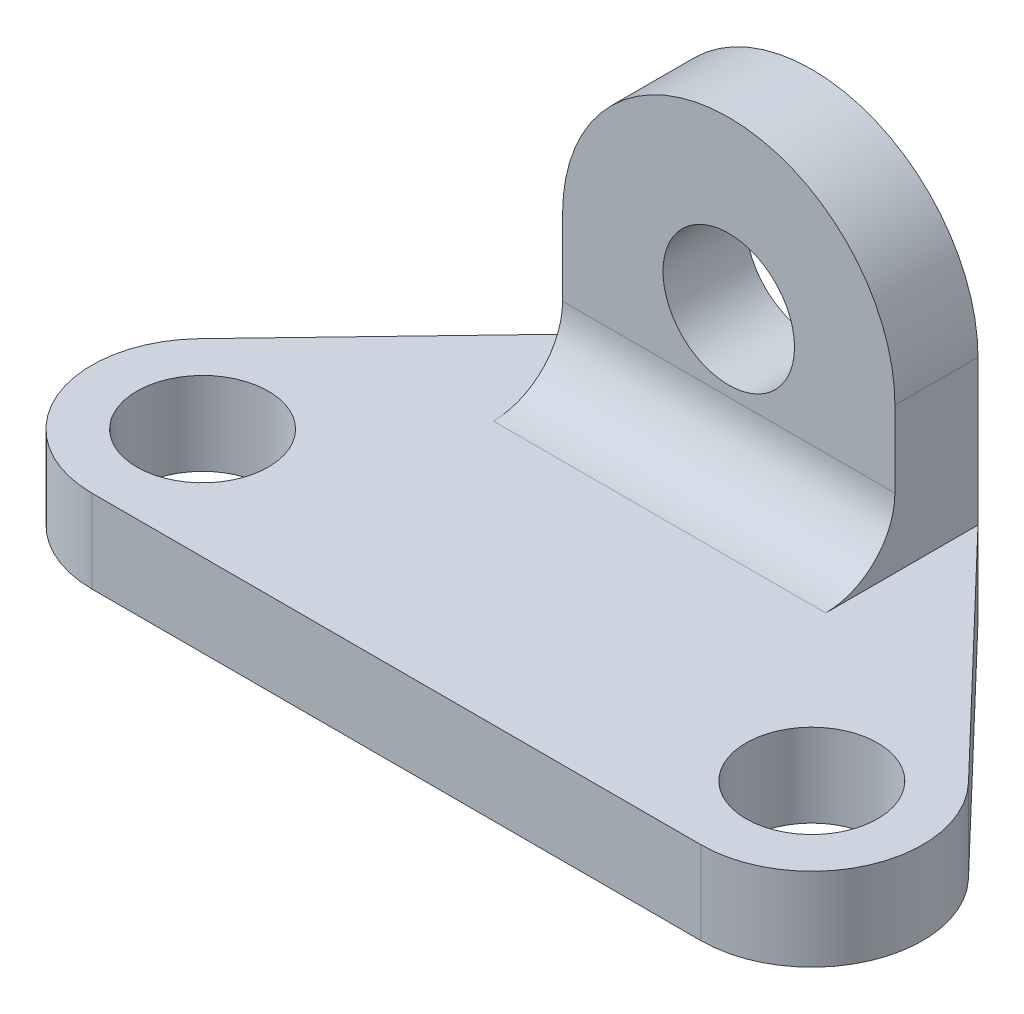
SolidWorks part; units mm, degrees
ref_plane "정면" through (0, 0, 0) normal (0, 0, 1) x (1, 0, 0)
ref_plane "윗면" through (0, 0, 0) normal (0, 1, 0) x (1, 0, 0)
ref_plane "우측면" through (0, 0, 0) normal (1, 0, 0) x (0, 0, -1)
sketch "스케치8" plane through (0, 0, 0) normal (0, 1, 0) x (1, 0, 0)
  line L0 (-44, -16) -> (44, -16)
  line L1 (-55.5528, 11.0695) -> (-24, 44)
  line L2 (-24, 44) -> (24, 44)
  line L3 (24, 44) -> (55.5528, 11.0695)
  arc A0 (-55.5528, 11.0695) -> (-44, -16) centre (-44, 0) ccw
  arc A1 (44, -16) -> (55.5528, 11.0695) centre (44, 0) ccw
  point P12 (44, 0)
  point P13 (41.7229, -13.9714)
  dimension "D1" = 32
  dimension "D2" = 32
  dimension "D8" = 0
  dimension "D3" = 44
  dimension "D4" = 44
  dimension "D5" = 48
  dimension "D6" = 24
  dimension "D10" = 44
extrude "보스-돌출3" add sketch "스케치8" along normal blind 12
sketch "스케치10" plane through (0, 0, 0) normal (0, 1, 0) x (1, 0, 0)
  circle A0 centre (-44, 0) radius 9.5
  circle A1 centre (44, 0) radius 9.5
  arc A2 (-55.5528, 11.0695) -> (-44, -16) centre (-44, 0) ccw construction
  arc A3 (44, -16) -> (55.5528, 11.0695) centre (44, 0) ccw construction
  dimension "D1" = 19
  dimension "D4" = 19
extrude "컷-돌출4" cut sketch "스케치10" along normal through all
sketch "스케치11" plane through (0, 0, -44) normal (0, 0, -1) x (-1, 0, 0)
  line L0 (24, 0) -> (55.5528, 0) construction
  line L2 (-24, 33) -> (-24, 0)
  line L3 (-24, 0) -> (24, 0)
  line L4 (24, 33) -> (24, 0)
  line L5 (-24, 33) -> (24, 0) construction
  line L6 (-24, 0) -> (24, 33) construction
  line L7 (24, 12) -> (24, 0) construction
  line L8 (-24, 12) -> (-24, 0) construction
  arc A0 (24, 33) -> (-24, 33) centre (0, 33) ccw
  point P0 (0, 16.5)
  point P8 (22, 33)
  point P14 (0, 0)
  point P15 (22, 33)
  point P16 (0, 0)
  dimension "D2" = 0
  dimension "D1" = 33
  dimension "D3" = 0
extrude "보스-돌출4" add sketch "스케치11" against normal blind 12 contours A0 L2 L3 L4
sketch "스케치12" plane through (0, 0, -32) normal (0, 0, 1) x (1, 0, 0)
  circle A0 centre (0, 33) radius 9.5
  arc A1 (24, 33) -> (-24, 33) centre (0, 33) ccw construction
  dimension "D1" = 19
extrude "컷-돌출5" cut sketch "스케치12" against normal blind 12
fillet "필렛1" radius 10 1 edges at (0, 12, -32)
